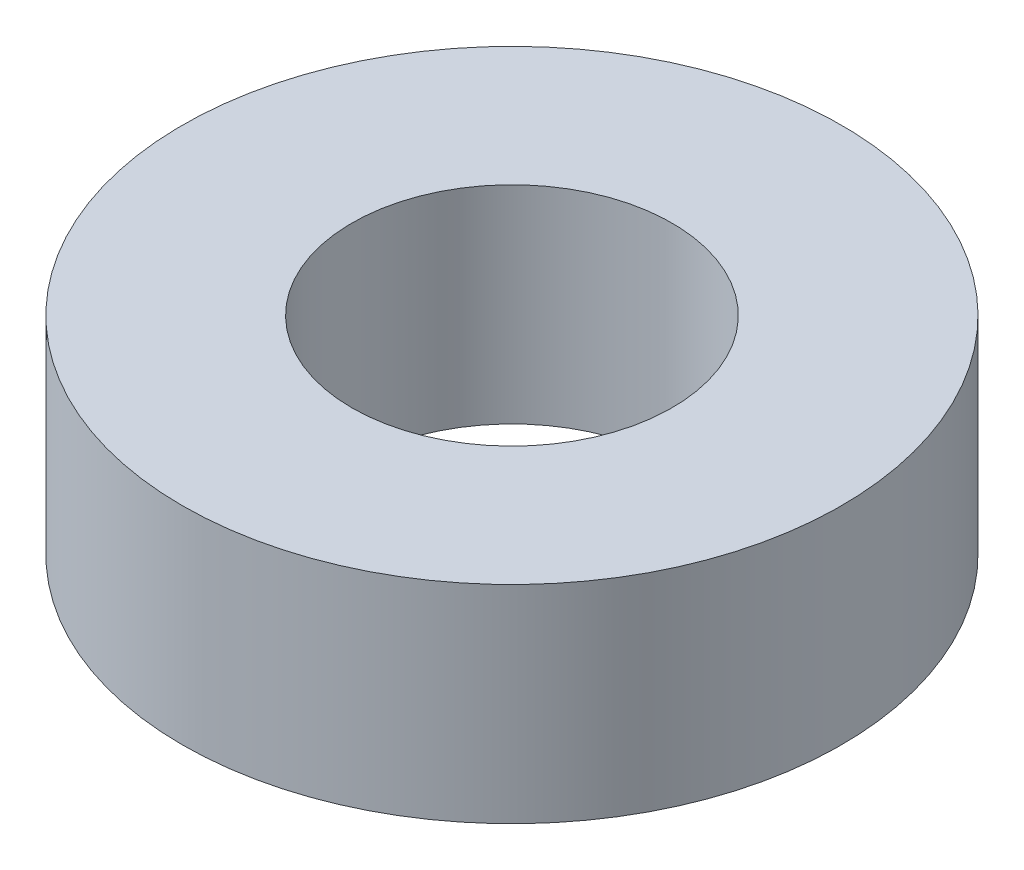
SolidWorks part; units mm, degrees
material "A286, generico"
ref_plane "Piano frontale" through (0, 0, 0) normal (0, 0, 1) x (1, 0, 0)
ref_plane "Piano superiore" through (0, 0, 0) normal (0, 1, 0) x (1, 0, 0)
ref_plane "Piano destro" through (0, 0, 0) normal (1, 0, 0) x (0, 0, -1)
sketch "Schizzo1" plane through (0, 0, 0) normal (0, 1, 0) x (1, 0, 0)
  circle A0 centre (0, 0) radius 17.5
  circle A1 centre (0, 0) radius 8.5
  dimension "D1" = 17
  dimension "D2" = 35
extrude "Estrusione-Estrusione1" add sketch "Schizzo1" along normal blind 11
